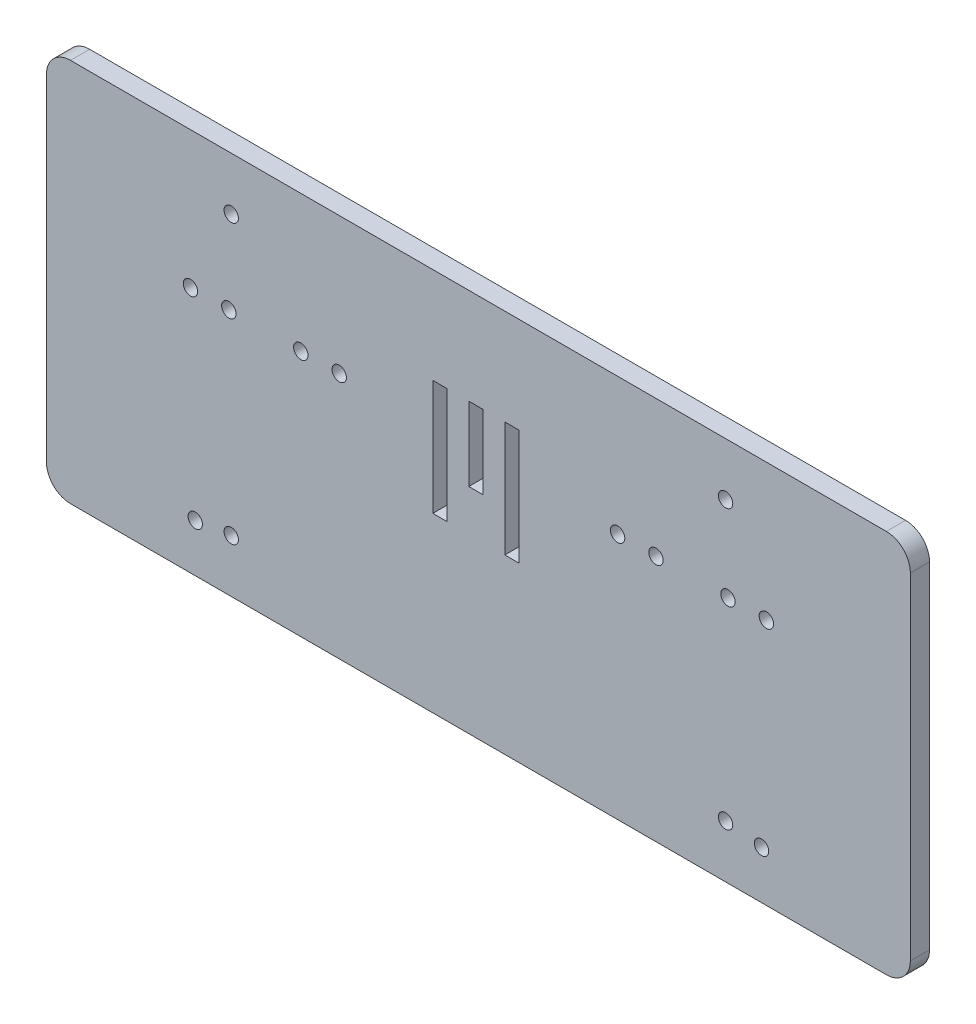
SolidWorks part; units mm, degrees
material "Acrylic (Medium-high impact)"
ref_plane "Front Plane" through (0, 0, 0) normal (0, 0, 1) x (1, 0, 0)
ref_plane "Top Plane" through (0, 0, 0) normal (0, 1, 0) x (1, 0, 0)
ref_plane "Right Plane" through (0, 0, 0) normal (1, 0, 0) x (0, 0, -1)
sketch "Sketch1" plane through (0, 0, 0) normal (0, 0, 1) x (1, 0, 0)
  line L2 (-87.2994, 18.8829) -> (92.7006, 18.8829)
  line L3 (-87.2994, 18.8829) -> (-87.2994, -61.1171)
  line L4 (-87.2994, -61.1171) -> (92.7006, -61.1171)
  line L5 (92.7006, 18.8829) -> (92.7006, -61.1171)
  circle A0 centre (-57.2994, -9.6171) radius 1.5
  circle A1 centre (62.7006, -9.6171) radius 1.5
  circle A2 centre (61.7006, -51.1171) radius 1.5
  circle A3 centre (-56.2994, -51.1171) radius 1.5
  circle A4 centre (-49.2994, -9.6171) radius 1.5
  circle A5 centre (54.7006, -9.6171) radius 1.5
  circle A6 centre (-34.2994, -9.6171) radius 1.5
  circle A7 centre (-26.2994, -9.6171) radius 1.5
  circle A8 centre (39.7006, -9.6171) radius 1.5
  circle A9 centre (31.7006, -9.6171) radius 1.5
  circle A10 centre (-48.7994, 7.8829) radius 1.5
  circle A11 centre (54.2006, 7.8829) radius 1.5
  circle A12 centre (54.2006, -50.1171) radius 1.5
  circle A13 centre (-48.7994, -50.1171) radius 1.5
  dimension "D1" = 30
  dimension "D10" = 180
  dimension "D11" = 8
  dimension "D12" = 8
  dimension "D13" = 8
  dimension "D15" = 8
  dimension "D16" = 2
  dimension "D17" = 15
  dimension "D14" = 15
  dimension "D20" = 11
  dimension "D2" = 31
  dimension "D3" = 31
  dimension "D4" = 30
  dimension "D5" = 28.5
  dimension "D6" = 28.5
  dimension "D7" = 80
  dimension "D8" = 10
  dimension "D9" = 10
  dimension "D19" = 38.5
  dimension "D18" = 2
extrude "Boss-Extrude1" add sketch "Sketch1" along normal blind 4
sketch "Sketch2" plane through (0, 0, 4) normal (0, 0, 1) x (1, 0, 0)
  line L1 (-6.7994, -1.1171) -> (-3.7994, -1.1171)
  line L2 (-6.7994, -1.1171) -> (-6.7994, -25.1171)
  line L3 (-6.7994, -25.1171) -> (-3.7994, -25.1171)
  line L4 (-3.7994, -1.1171) -> (-3.7994, -25.1171)
  line L5 (0.7006, -1.1171) -> (3.7006, -1.1171)
  line L6 (0.7006, -1.1171) -> (0.7006, -16.5171)
  line L7 (0.7006, -16.5171) -> (3.7006, -16.5171)
  line L8 (3.7006, -1.1171) -> (3.7006, -16.5171)
  line L12 (11.2006, -1.1171) -> (11.2006, -25.1171)
  line L13 (8.2006, -1.1171) -> (11.2006, -1.1171)
  line L14 (8.2006, -1.1171) -> (8.2006, -25.1171)
  line L15 (8.2006, -25.1171) -> (11.2006, -25.1171)
  line L16 (92.7006, 18.8829) -> (-87.2994, 18.8829) construction
  dimension "D1" = 20
  dimension "D2" = 2
  dimension "D4" = 20
extrude "Cut-Extrude1" cut sketch "Sketch2" against normal blind 4
fillet "Fillet1" radius 5 4 edges at (-87.2994, 18.8829, 2) (-87.2994, -61.1171, 2) (92.7006, -61.1171, 2) (92.7006, 18.8829, 2)
